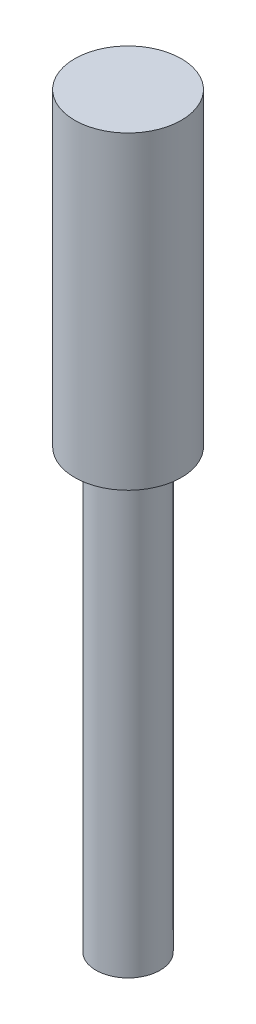
SolidWorks part; units mm, degrees
ref_plane "Front" through (0, 0, 0) normal (0, 0, 1) x (1, 0, 0)
ref_plane "Top" through (0, 0, 0) normal (0, 1, 0) x (1, 0, 0)
ref_plane "Right" through (0, 0, 0) normal (1, 0, 0) x (0, 0, -1)
sketch "Sketch1" plane through (0, 0, 0) normal (0, 1, 0) x (1, 0, 0)
  circle A0 centre (0, 0) radius 5
  dimension "D1" = 10
extrude "Boss-Extrude1" add sketch "Sketch1" along normal blind 70
sketch "Sketch2" plane through (0, 0, 0) normal (0, -1, 0) x (-1, 0, 0)
  circle A0 centre (0, 0) radius 3
  circle A1 centre (0, 0) radius 5
  circle A2 centre (0, 0) radius 5 construction
  dimension "D1" = 6
extrude "Cut-Extrude1" cut sketch "Sketch2" against normal blind 41
